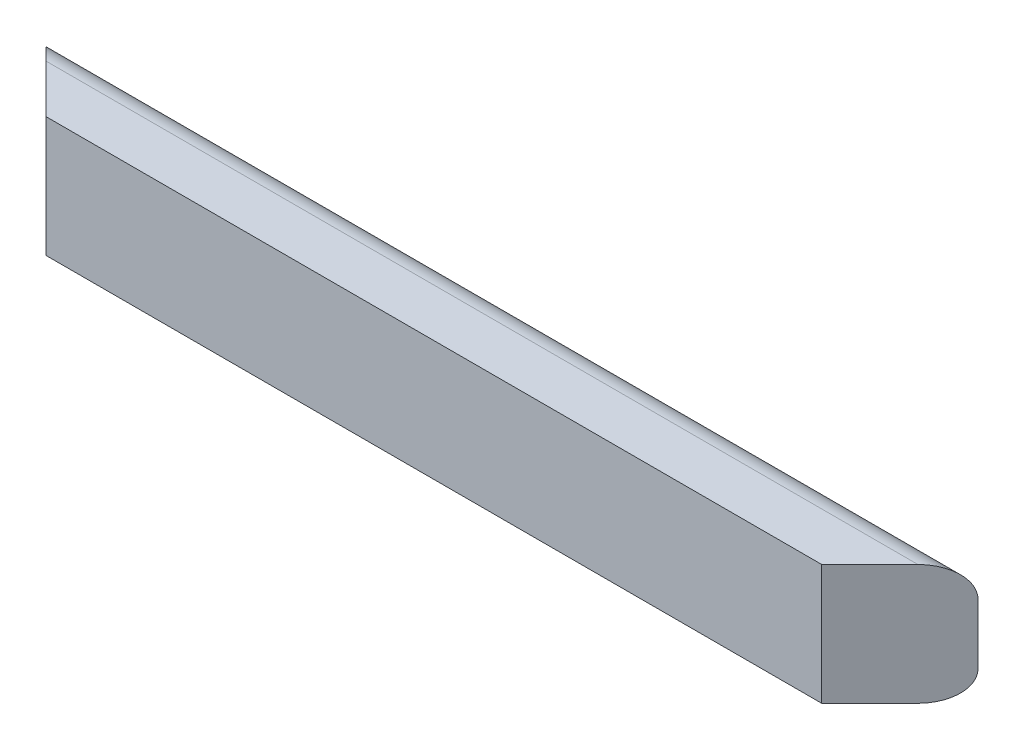
SolidWorks part; units mm, degrees
ref_plane "Front" through (0, 0, 0) normal (0, 0, 1) x (1, 0, 0)
ref_plane "Top" through (0, 0, 0) normal (0, 1, 0) x (1, 0, 0)
ref_plane "Right" through (0, 0, 0) normal (1, 0, 0) x (0, 0, -1)
sketch "Sketch1" plane through (0, 0, 0) normal (1, 0, 0) x (0, 0, -1)
  line L0 (0, 0) -> (0, 127) construction
  line L1 (0, 0) -> (31.75, 0)
  line L2 (31.75, 127) -> (0, 127)
  line L3 (63.5, 95.25) -> (63.5, 31.75)
  line L4 (0, 0) -> (-19.05, 0)
  line L5 (-19.05, 0) -> (-19.05, 127)
  line L6 (-19.05, 127) -> (0, 127)
  arc A0 (31.75, 0) -> (63.5, 31.75) centre (31.75, 31.75) ccw
  arc A1 (63.5, 95.25) -> (31.75, 127) centre (31.75, 95.25) ccw
  dimension "D2" = 63.5
  dimension "D1" = 19.05
extrude "Boss-Extrude1" add sketch "Sketch1" along normal blind 984.25
ref_plane "Mid_Plane" through (492.125, 0, 0) normal (1, 0, 0) x (0, 0, -1)
ref_plane "Plane1" through (460.375, 0, 460.375) normal (0.7071, 0, 0.7071) x (0, 1, 0)
sketch "Sketch2" plane through (460.375, 0, 460.375) normal (0.7071, 0, 0.7071) x (0, 1, 0)
  line L1 (205.1964, -433.0743) -> (-139.2061, -433.0743)
  line L2 (205.1964, -433.0743) -> (205.1964, -926.2875)
  line L3 (205.1964, -926.2875) -> (-139.2061, -926.2875)
  line L4 (-139.2061, -433.0743) -> (-139.2061, -926.2875)
  line L5 (205.1964, -433.0743) -> (-139.2061, -926.2875) construction
  line L6 (205.1964, -926.2875) -> (-139.2061, -433.0743) construction
  point P4 (32.9952, -679.6809)
extrude "Cut-Extrude1" cut sketch "Sketch2" along normal through all
mirror "Mirror1" about plane through (492.125, 0, 0) normal (1, 0, 0) of "Cut-Extrude1"
